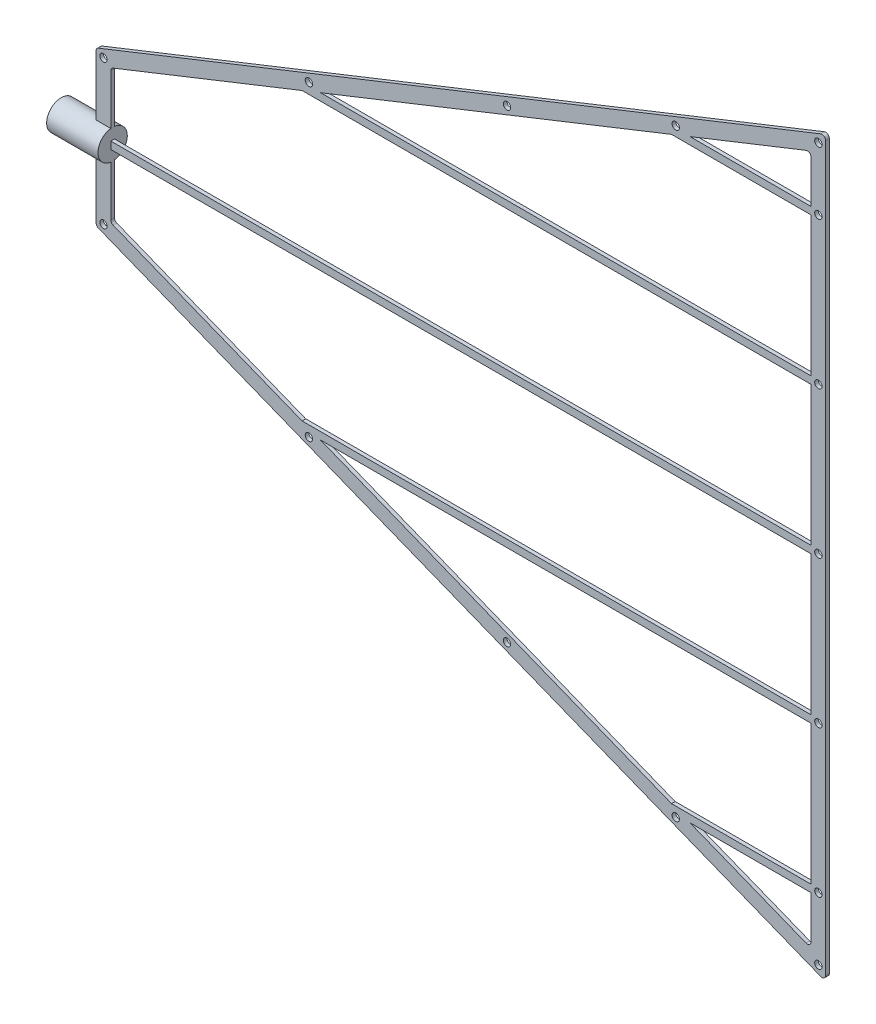
SolidWorks part; units mm, degrees
material "普通碳钢"
ref_plane "前视基准面" through (0, 0, 0) normal (0, 0, 1) x (1, 0, 0)
ref_plane "上视基准面" through (0, 0, 0) normal (0, 1, 0) x (1, 0, 0)
ref_plane "右视基准面" through (0, 0, 0) normal (1, 0, 0) x (0, 0, -1)
sketch "草图1" plane through (0, 0, 0) normal (0, 0, 1) x (1, 0, 0)
  line L0 (0, -10.5) -> (0, 10.5)
  line L1 (0, 10.5) -> (99.4422, 50)
  line L2 (99.4422, 50) -> (99.4422, -50)
  line L3 (99.4422, -50) -> (0, -10.5)
  line L4 (0, 0) -> (99.4422, 0) construction
  line L5 (2, 9.1424) -> (28.0754, 19.5)
  line L6 (97.4422, 47.0536) -> (97.4422, 40.5)
  line L7 (97.4422, -47.0536) -> (80.9434, -40.5)
  line L8 (2, -9.1424) -> (2, -0.5)
  line L9 (2, 0.5) -> (97.4422, 0.5)
  line L10 (2, -0.5) -> (97.4422, -0.5)
  line L11 (28.0754, 19.5) -> (97.4422, 19.5)
  line L12 (30.593, 20.5) -> (97.4422, 20.5)
  line L13 (78.4259, 39.5) -> (97.4422, 39.5)
  line L14 (28.0754, 20.5) -> (97.4422, 20.5) construction
  line L15 (80.9434, 40.5) -> (97.4422, 40.5)
  line L16 (80.9434, -40.5) -> (97.4422, -40.5)
  line L17 (78.4259, 40.5) -> (97.4422, 40.5) construction
  line L18 (78.4259, -39.5) -> (97.4422, -39.5)
  line L19 (30.593, -20.5) -> (97.4422, -20.5)
  line L20 (28.0754, -19.5) -> (97.4422, -19.5)
  line L21 (97.4422, 39.5) -> (97.4422, 20.5)
  line L22 (80.9434, 40.5) -> (97.4422, 47.0536)
  line L23 (97.4422, 47.0536) -> (97.4422, -47.0536) construction
  line L24 (97.4422, 19.5) -> (97.4422, 0.5)
  line L25 (2, 9.1424) -> (97.4422, 47.0536) construction
  line L26 (30.593, 20.5) -> (78.4259, 39.5)
  line L27 (2, 0.5) -> (2, 9.1424)
  line L28 (97.4422, -0.5) -> (97.4422, -19.5)
  line L29 (2, -9.1424) -> (2, 9.1424) construction
  line L30 (97.4422, -20.5) -> (97.4422, -39.5)
  line L31 (28.0754, -19.5) -> (2, -9.1424)
  line L32 (78.4259, -39.5) -> (30.593, -20.5)
  line L33 (97.4422, -47.0536) -> (2, -9.1424) construction
  line L34 (97.4422, -40.5) -> (97.4422, -47.0536)
  point P4 (0, 0)
  dimension "D1" = 21
  dimension "D2" = 107
  dimension "D3" = 100
  dimension "D5" = 1
  dimension "D6" = 19.5
  dimension "D8" = 39.5
  dimension "D4" = 2
  dimension "D7" = 1
  dimension "D9" = 1
extrude "凸台-拉伸1" add sketch "草图1" along normal mid plane 0.5
sketch "草图4" plane through (0, 0, 0) normal (0, 0, 1) x (1, 0, 0)
  line L10 (80.9434, 40.5) -> (97.4422, 40.5) construction
  line L11 (30.593, 20.5) -> (97.4422, 20.5) construction
  line L12 (0, 0) -> (11.7687, 0) construction
  line L14 (1, -9.8212) -> (98.4422, -48.5268)
  line L15 (98.4422, -48.5268) -> (98.4422, 48.5268)
  line L16 (98.4422, 48.5268) -> (1, 9.8212)
  line L17 (1, 9.8212) -> (1, -9.8212)
  line L18 (1, -9.8212) -> (98.4422, -48.5268) construction
  line L19 (98.4422, -48.5268) -> (98.4422, 48.5268) construction
  line L20 (98.4422, 48.5268) -> (1, 9.8212) construction
  line L21 (1, 9.8212) -> (1, -9.8212) construction
  circle A0 centre (1, 9.8212) radius 0.5
  circle A1 centre (29, 20.9433) radius 0.5
  circle A2 centre (56, 31.6681) radius 0.5
  circle A3 centre (79, 40.804) radius 0.5
  circle A4 centre (98.4422, 48.5268) radius 0.5
  circle A5 centre (98.4422, 40) radius 0.5
  circle A6 centre (98.4422, 20) radius 0.5
  circle A7 centre (98.4422, 0) radius 0.5
  circle A8 centre (98.4422, -20) radius 0.5
  circle A9 centre (98.4422, -40) radius 0.5
  circle A10 centre (98.4422, -48.5268) radius 0.5
  circle A11 centre (79, -40.804) radius 0.5
  circle A12 centre (56, -31.6681) radius 0.5
  circle A13 centre (29, -20.9433) radius 0.5
  circle A14 centre (1, -9.8212) radius 0.5
  dimension "D2" = 1
  dimension "D3" = 28
  dimension "D4" = 55
  dimension "D5" = 78
  dimension "D6" = 0.5
  dimension "D7" = 0.5
  dimension "D1" = 1
extrude "切除-拉伸1" cut sketch "草图4" against normal mid plane 0.5
sketch "草图5" plane through (0, 0, 0) normal (0, 0, 1) x (1, 0, 0)
  line L0 (0, 0) -> (-17.3027, 0) construction
  line L1 (2, 0) -> (2, 2)
  line L2 (2, 9.1424) -> (2, 0.5) construction
  line L3 (2, 2) -> (-5, 2)
  line L4 (-5, 2) -> (-5, 1.9)
  line L5 (-5, 1.9) -> (0, 1.9)
  line L6 (0, 10.5) -> (0, -10.5) construction
  line L7 (0, 1.9) -> (0, 0)
  line L8 (0, 0) -> (2, 0)
  dimension "D1" = 7
  dimension "D2" = 4
  dimension "D3" = 3.8
revolve "旋转1" add sketch "草图5" angle 360 about L0
fillet "圆角1" radius 0.5 8 edges at (97.4422, 47.0536, 0) (99.4422, 50, 0) (97.4422, -47.0536, 0) (99.4422, -50, 0) (2, 9.1424, 0) (2, -9.1424, 0) (0, -10.5, 0) (0, 10.5, 0)
